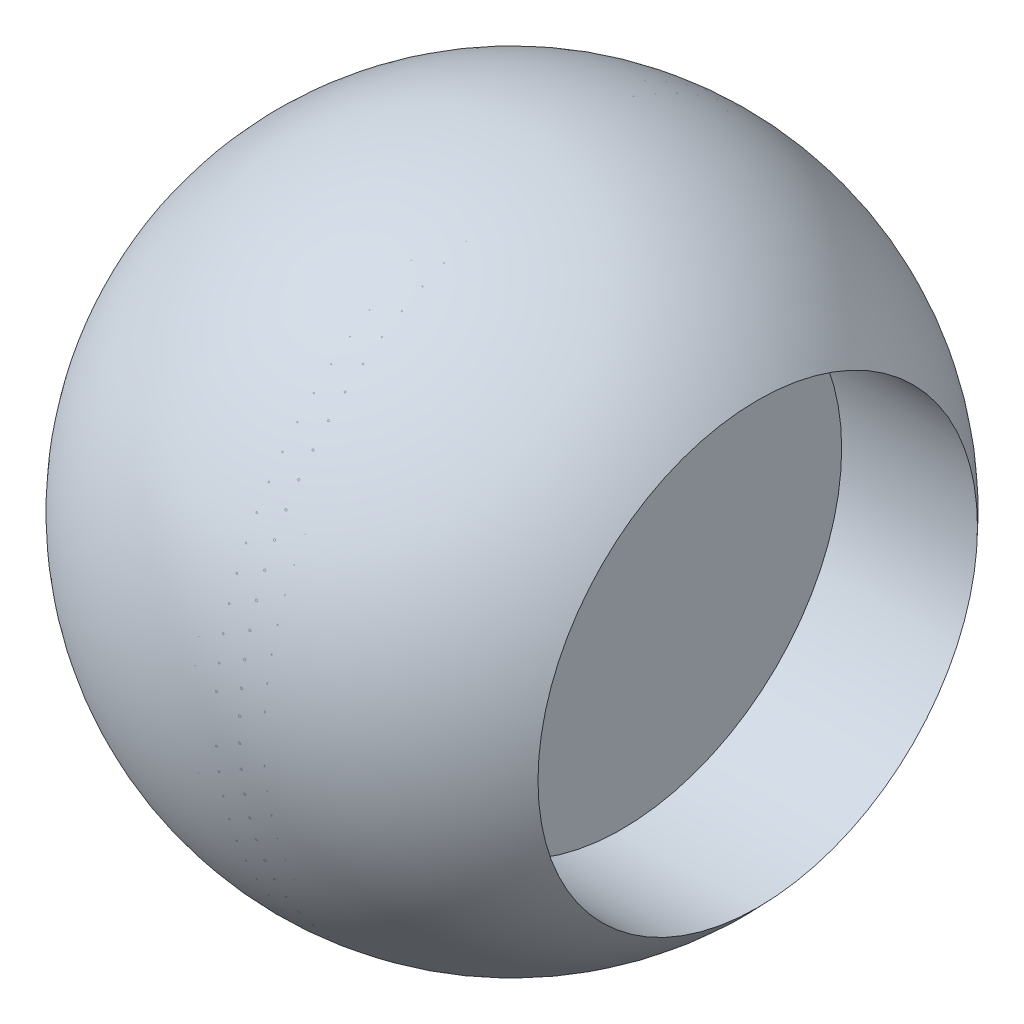
SolidWorks part; units mm, degrees
ref_plane "Front Plane" through (0, 0, 0) normal (0, 0, 1) x (1, 0, 0)
ref_plane "Top Plane" through (0, 0, 0) normal (0, 1, 0) x (1, 0, 0)
ref_plane "Right Plane" through (0, 0, 0) normal (1, 0, 0) x (0, 0, -1)
sketch "Sketch1" plane through (0, 0, 0) normal (0, 0, 1) x (1, 0, 0)
  line L0 (0, 22.5) -> (0, -22.5)
  arc A0 (0, 22.5) -> (0, -22.5) centre (0, 0) cw
  dimension "D2" = 22.5
  dimension "D1" = 45
revolve "Revolve1" add sketch "Sketch1" angle 360 about L0
sketch "Sketch2" plane through (0, 0, 0) normal (0, 0, 1) x (1, 0, 0)
  line L0 (0, 22.5) -> (0, 0) construction
  line L1 (5, 19.9178) -> (-5, 19.9178)
  line L2 (5, 19.9178) -> (5, 21.9178)
  line L4 (-5, 19.9178) -> (-5, 21.9178)
  line L5 (0.0966, 22.4807) -> (0, 22.5) construction
  line L6 (0, 22.5) -> (-0.0966, 22.4807) construction
  line L7 (0, 0) -> (-22.5, 0) construction
  circle A0 centre (0, 0) radius 22.5 construction
  arc A1 (5, 21.9178) -> (-5, 21.9178) centre (0, 0) ccw
  point P0 (0, 22.5)
  dimension "D1" = 2
  dimension "D2" = 10
  dimension "D3" = 21.9178
  dimension "D4" = 21.9178
revolve "Cut-Revolve6" cut sketch "Sketch2" angle 360 about L7
ref_plane "Plane2" through (22.5, 0, 0) normal (1, 0, 0) x (0, 0, -1)
sketch "Sketch4" plane through (22.5, 0, 0) normal (1, 0, 0) x (0, 0, -1)
  circle A0 centre (0, 0) radius 15
  dimension "D1" = 30
extrude "Cut-Extrude1" cut sketch "Sketch4" against normal blind 15
